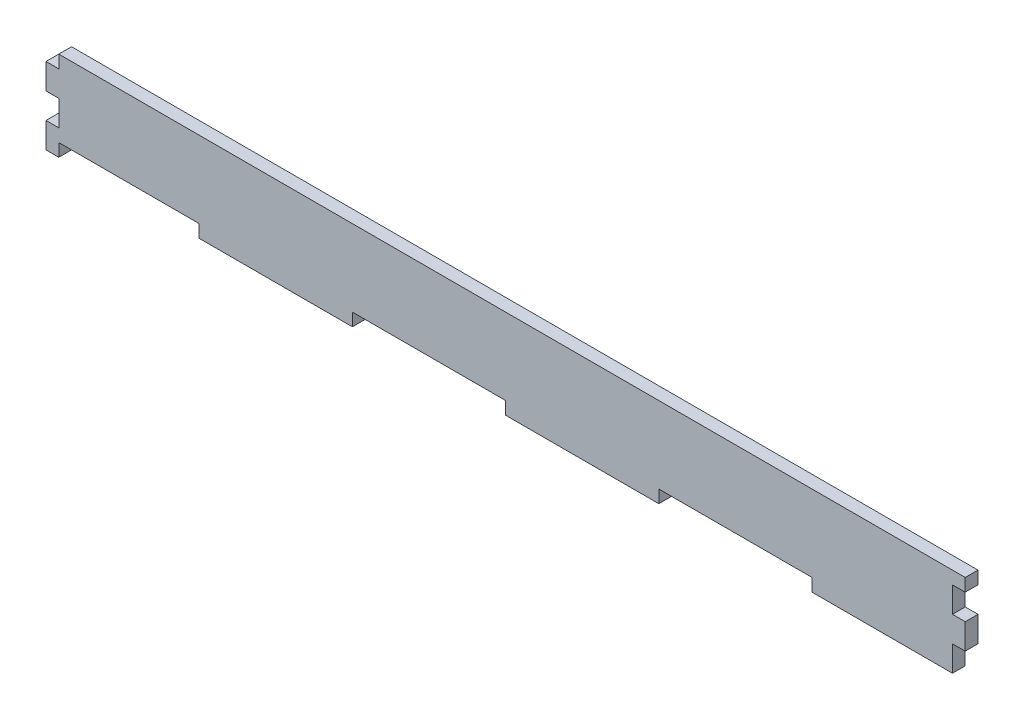
SolidWorks part; units mm, degrees
material "Acrylic (Medium-high impact)"
ref_plane "Front Plane" through (0, 0, 0) normal (0, 0, 1) x (1, 0, 0)
ref_plane "Top Plane" through (0, 0, 0) normal (0, 1, 0) x (1, 0, 0)
ref_plane "Right Plane" through (0, 0, 0) normal (1, 0, 0) x (0, 0, -1)
sketch "Sketch1" plane through (0, 0, 0) normal (0, 0, 1) x (1, 0, 0)
  line L0 (-76.2, 12.7) -> (-76.2, 9.525)
  line L1 (-114.3, 12.7) -> (114.3, 12.7)
  line L2 (-114.3, 12.7) -> (-114.3, -12.7)
  line L3 (-114.3, -12.7) -> (114.3, -12.7)
  line L4 (114.3, 12.7) -> (114.3, -12.7)
  line L5 (-114.3, 12.7) -> (-76.2, 12.7)
  line L6 (-114.3, 12.7) -> (-114.3, 9.525)
  line L7 (-114.3, 9.525) -> (-76.2, 9.525)
  line L8 (-76.2, 12.7) -> (-76.2, 9.525)
  line L9 (-76.2, 12.7) -> (-38.1, 12.7)
  line L10 (-38.1, 12.7) -> (-38.1, 9.525)
  line L11 (-76.2, 9.525) -> (-38.1, 9.525)
  line L12 (-38.1, 12.7) -> (-38.1, 9.525)
  line L13 (-38.1, 12.7) -> (0, 12.7)
  line L14 (0, 12.7) -> (0, 9.525)
  line L15 (-38.1, 9.525) -> (0, 9.525)
  line L16 (0, 12.7) -> (0, 9.525)
  line L17 (0, 12.7) -> (38.1, 12.7)
  line L18 (38.1, 12.7) -> (38.1, 9.525)
  line L19 (0, 9.525) -> (38.1, 9.525)
  line L20 (38.1, 12.7) -> (38.1, 9.525)
  line L21 (38.1, 12.7) -> (76.2, 12.7)
  line L22 (76.2, 12.7) -> (76.2, 9.525)
  line L23 (38.1, 9.525) -> (76.2, 9.525)
  line L24 (76.2, 12.7) -> (76.2, 9.525)
  line L25 (76.2, 12.7) -> (114.3, 12.7)
  line L26 (114.3, 12.7) -> (114.3, 9.525)
  line L27 (76.2, 9.525) -> (114.3, 9.525)
  line L76 (-76.2, -12.7) -> (-76.2, -9.525)
  line L77 (-114.3, -12.7) -> (-76.2, -12.7)
  line L78 (-114.3, -12.7) -> (-114.3, -9.525)
  line L79 (-114.3, -9.525) -> (-76.2, -9.525)
  line L80 (-76.2, -12.7) -> (-76.2, -9.525)
  line L81 (-76.2, -12.7) -> (-38.1, -12.7)
  line L82 (-38.1, -12.7) -> (-38.1, -9.525)
  line L83 (-76.2, -9.525) -> (-38.1, -9.525)
  line L84 (-38.1, -12.7) -> (-38.1, -9.525)
  line L85 (-38.1, -12.7) -> (0, -12.7)
  line L86 (0, -12.7) -> (0, -9.525)
  line L87 (-38.1, -9.525) -> (0, -9.525)
  line L88 (0, -12.7) -> (0, -9.525)
  line L89 (0, -12.7) -> (38.1, -12.7)
  line L90 (38.1, -12.7) -> (38.1, -9.525)
  line L91 (0, -9.525) -> (38.1, -9.525)
  line L92 (38.1, -12.7) -> (38.1, -9.525)
  line L93 (38.1, -12.7) -> (76.2, -12.7)
  line L94 (76.2, -12.7) -> (76.2, -9.525)
  line L95 (38.1, -9.525) -> (76.2, -9.525)
  line L96 (76.2, -12.7) -> (76.2, -9.525)
  line L97 (76.2, -12.7) -> (114.3, -12.7)
  line L98 (114.3, -12.7) -> (114.3, -9.525)
  line L99 (76.2, -9.525) -> (114.3, -9.525)
  line L148 (-114.3, 6.35) -> (-114.3, 0)
  line L149 (-114.3, 12.7) -> (-111.125, 12.7)
  line L150 (-114.3, 12.7) -> (-114.3, 6.35)
  line L151 (-114.3, 6.35) -> (-111.125, 6.35)
  line L152 (-111.125, 12.7) -> (-111.125, 6.35)
  line L153 (-114.3, 6.35) -> (-111.125, 6.35)
  line L154 (-111.125, 6.35) -> (-111.125, 0)
  line L155 (-114.3, 0) -> (-111.125, 0)
  line L156 (-114.3, 0) -> (-114.3, -6.35)
  line L157 (-114.3, 0) -> (-111.125, 0)
  line L158 (-111.125, 0) -> (-111.125, -6.35)
  line L159 (-114.3, -6.35) -> (-111.125, -6.35)
  line L160 (-114.3, -6.35) -> (-114.3, -12.7)
  line L161 (-114.3, -6.35) -> (-111.125, -6.35)
  line L162 (-111.125, -6.35) -> (-111.125, -12.7)
  line L163 (-114.3, -12.7) -> (-111.125, -12.7)
  line L164 (114.3, 6.35) -> (114.3, 0)
  line L165 (114.3, 12.7) -> (111.125, 12.7)
  line L166 (114.3, 12.7) -> (114.3, 6.35)
  line L167 (114.3, 6.35) -> (111.125, 6.35)
  line L168 (111.125, 12.7) -> (111.125, 6.35)
  line L169 (114.3, 6.35) -> (111.125, 6.35)
  line L170 (111.125, 6.35) -> (111.125, 0)
  line L171 (114.3, 0) -> (111.125, 0)
  line L172 (114.3, 0) -> (114.3, -6.35)
  line L173 (114.3, 0) -> (111.125, 0)
  line L174 (111.125, 0) -> (111.125, -6.35)
  line L175 (114.3, -6.35) -> (111.125, -6.35)
  line L176 (114.3, -6.35) -> (114.3, -12.7)
  line L177 (114.3, -6.35) -> (111.125, -6.35)
  line L178 (111.125, -6.35) -> (111.125, -12.7)
  line L179 (114.3, -12.7) -> (111.125, -12.7)
  point P4 (-114.3, 0)
  point P6 (0, 12.7)
  dimension "D1" = 228.6
  dimension "D2" = 25.4
  dimension "D3" = 38.1
  dimension "D4" = 3.175
  dimension "D7" = 6.35
  dimension "D8" = 3.175
  dimension "D5" = 6
  dimension "D6" = 6
  dimension "D9" = 4
  dimension "D10" = 4
extrude "Boss-Extrude1" add sketch "Sketch1" along normal blind 3.175 contours L178 L99 L94 L3 | L91 L86 L3 L90 | L83 L76 L3 L82 | L162 L79 L2 L3 | L162 L159 L2 L79 | L2 L155 L154 L151 | L175 L4 L171 L174 | L27 L168 L167 L4 | L178 L174 L170 L168 L27 L23 L19 L15 L11 L7 L152 L154 L158 L162 L79 L83 L87 L91 L95 L99
equation "\"D3@Sketch1\"=\"D1@Sketch1\"/\"D5@Sketch1\""
